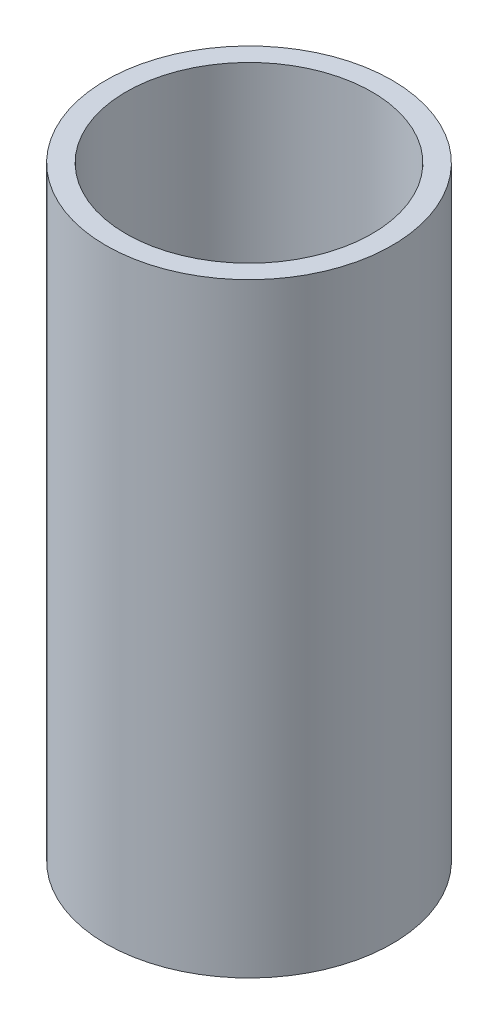
SolidWorks part; units mm, degrees
ref_plane "Front Plane" through (0, 0, 0) normal (0, 0, 1) x (1, 0, 0)
ref_plane "Top Plane" through (0, 0, 0) normal (0, 1, 0) x (1, 0, 0)
ref_plane "Right Plane" through (0, 0, 0) normal (1, 0, 0) x (0, 0, -1)
sketch "Sketch1" plane through (0, 0, 0) normal (0, 1, 0) x (1, 0, 0)
  circle A0 centre (0, 0) radius 7.1
  circle A1 centre (0, 0) radius 6.1
extrude "Boss-Extrude1" add sketch "Sketch1" along normal blind 30
